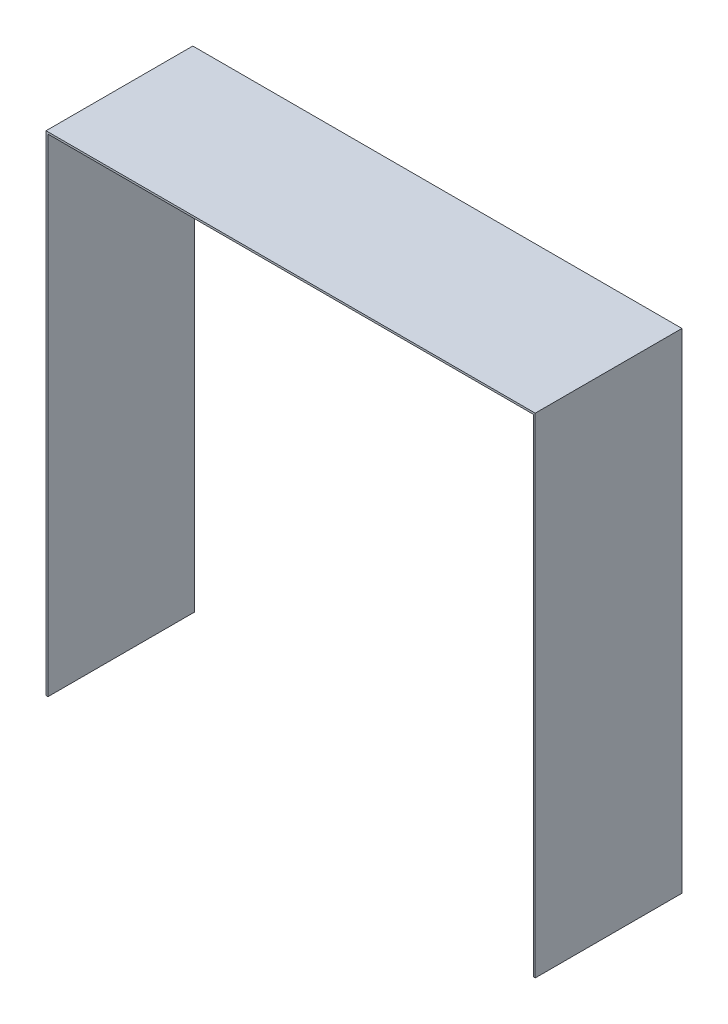
SolidWorks part; units mm, degrees
ref_plane "Front Plane" through (0, 0, 0) normal (0, 0, 1) x (1, 0, 0)
ref_plane "Top Plane" through (0, 0, 0) normal (0, 1, 0) x (1, 0, 0)
ref_plane "Right Plane" through (0, 0, 0) normal (1, 0, 0) x (0, 0, -1)
sketch "Sketch1" plane through (0, 0, 0) normal (0, 0, 1) x (1, 0, 0)
  line L0 (0, 0) -> (2, 0)
  line L1 (2, 0) -> (2, 498)
  line L2 (2, 498) -> (498, 498)
  line L3 (498, 498) -> (498, 0)
  line L4 (498, 0) -> (500, 0)
  line L5 (500, 0) -> (500, 500)
  line L6 (500, 500) -> (0, 500)
  line L7 (0, 500) -> (0, 0)
  dimension "D1" = 2
  dimension "D2" = 2
  dimension "D3" = 500
  dimension "D4" = 500
  dimension "D5" = 2
extrude "Boss-Extrude1" add sketch "Sketch1" along normal blind 150
